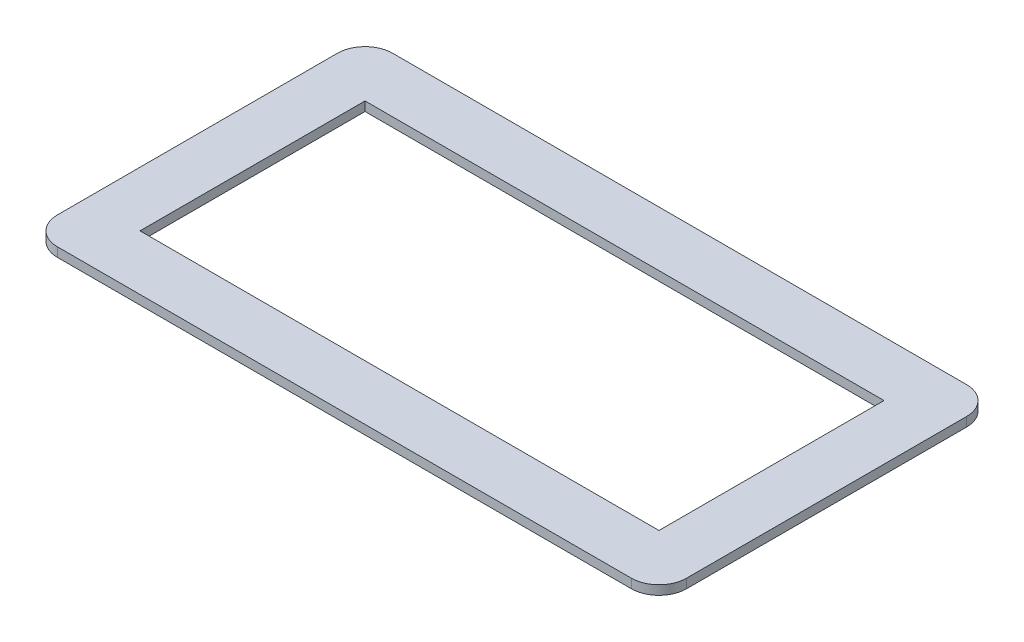
SolidWorks part; units mm, degrees
ref_plane "前视基准面" through (0, 0, 0) normal (0, 0, 1) x (1, 0, 0)
ref_plane "上视基准面" through (0, 0, 0) normal (0, 1, 0) x (1, 0, 0)
ref_plane "右视基准面" through (0, 0, 0) normal (1, 0, 0) x (0, 0, -1)
sketch "草图1" plane through (0, 0, 0) normal (0, 1, 0) x (1, 0, 0)
  line L0 (-159.1275, 66.9412) -> (-90.6275, 66.9412)
  line L1 (-153.1275, 60.9412) -> (-96.6275, 60.9412)
  line L2 (-153.1275, 60.9412) -> (-153.1275, 36.4412)
  line L3 (-153.1275, 36.4412) -> (-96.6275, 36.4412)
  line L4 (-96.6275, 60.9412) -> (-96.6275, 36.4412)
  line L5 (-90.6275, 66.9412) -> (-90.6275, 30.4412)
  line L6 (-159.1275, 30.4412) -> (-90.6275, 30.4412)
  line L7 (-159.1275, 66.9412) -> (-159.1275, 30.4412)
  dimension "D1" = 56.5
  dimension "D2" = 24.5
  dimension "D3" = 6
extrude "凸台-拉伸1" add sketch "草图1" along normal blind 1
fillet "圆角1" radius 3 4 edges at (-90.6275, 0.5, -66.9412) (-90.6275, 0.5, -30.4412) (-159.1275, 0.5, -30.4412) (-159.1275, 0.5, -66.9412)
